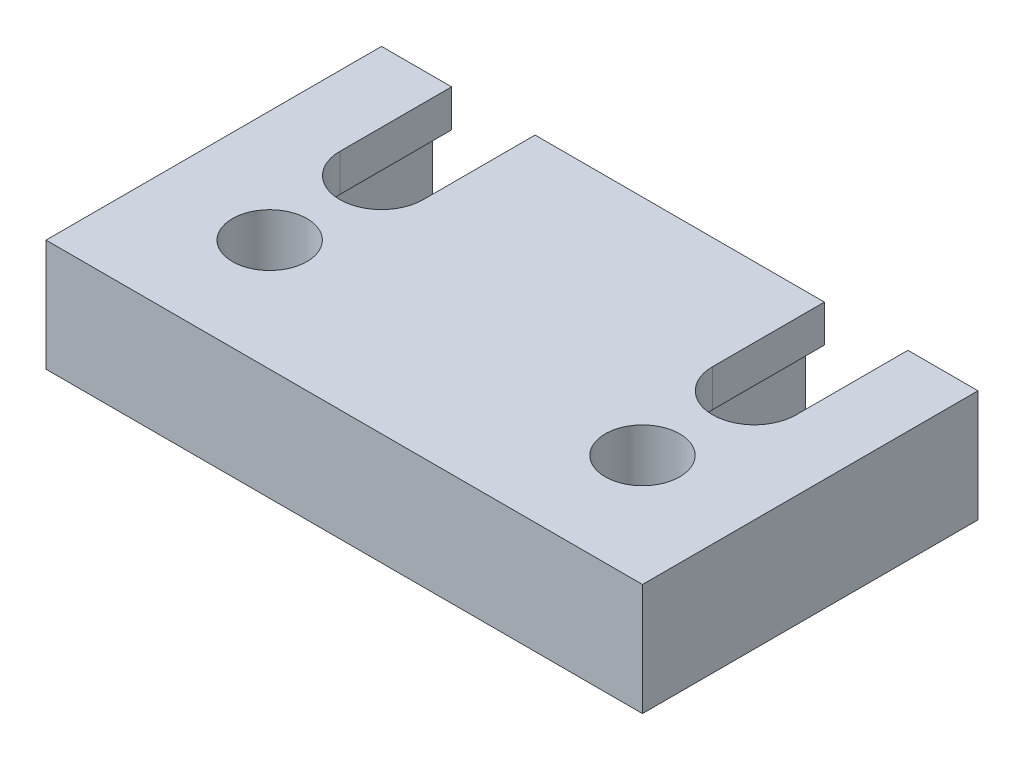
SolidWorks part; units mm, degrees
material "AISI 1018 Steel Cold Rolled"
ref_plane "Plane1" through (0, 0, 0) normal (0, 0, 1) x (1, 0, 0)
ref_plane "Plane2" through (0, 0, 0) normal (0, 1, 0) x (1, 0, 0)
ref_plane "Plane3" through (0, 0, 0) normal (1, 0, 0) x (0, 0, -1)
sketch "Sketch1" plane through (0, 0, 0) normal (0, 1, 0) x (1, 0, 0)
  line L0 (57.15, 76.2) -> (57.15, 0) construction
  line L1 (0, 0) -> (114.3, 0)
  line L2 (0, 0) -> (0, 76.2)
  line L3 (0, 76.2) -> (114.3, 76.2)
  line L4 (114.3, 0) -> (114.3, 76.2)
  line L5 (96.012, 63.5) -> (96.012, 38.1)
  line L6 (18.288, 63.5) -> (18.288, 38.1)
  line L7 (32.512, 63.5) -> (32.512, 38.1)
  line L8 (81.788, 63.5) -> (81.788, 38.1)
  line L9 (18.288, 50.8) -> (32.512, 50.8) construction
  line L10 (96.012, 50.8) -> (81.788, 50.8) construction
  arc A0 (32.512, 63.5) -> (18.288, 63.5) centre (25.4, 63.5) ccw
  arc A1 (18.288, 38.1) -> (32.512, 38.1) centre (25.4, 38.1) ccw
  arc A4 (96.012, 38.1) -> (81.788, 38.1) centre (88.9, 38.1) cw
  arc A5 (81.788, 63.5) -> (96.012, 63.5) centre (88.9, 63.5) cw
  dimension "D3" = 14.224
  dimension "D7" = 63.5
  dimension "D1" = 76.2
  dimension "D2" = 114.3
  dimension "D4" = 25.4
  dimension "D5" = 25.4
  dimension "D8" = 25.4
extrude "Base-Extrude" add sketch "Sketch1" along normal blind 19.05
hole_wizard "1/2-20 Tapped Hole1" positions "Sketch3" profile "Sketch2" tap size "1/2-20" standard "Ansi Inch" end condition through all
sketch "Sketch3" plane through (0, 19.05, 0) normal (0, 1, 0) x (-1, 0, 0)
  line L0 (0, 0) -> (-114.3, 0) construction
  line L2 (-114.3, 0) -> (-114.3, -76.2) construction
  point P0 (-25.4, -19.05)
  point P1 (-88.9, -19.05)
  dimension "D1" = 19.05
  dimension "D2" = 19.05
  dimension "D3" = 88.9
  dimension "D4" = 25.4
sketch "Sketch2" plane through (25.4, 19.05, -19.05) normal (1, 0, 0) x (0, 0, 1)
  line L0 (0, 0) -> (0, 19.05)
  line L1 (0, 19.05) -> (6.35, 19.05)
  line L2 (6.35, 19.05) -> (6.35, 0)
  line L5 (6.35, 0) -> (0, 0)
  line L11 (0, -6.35) -> (0, 107.95) construction
  dimension "Thread Major Dia." = 12.7
  dimension "Thru Tap Drill Depth" = 19.05
ref_plane "Plane4" through (133.35, 0, 0) normal (1, 0, 0) x (0, 0, -1)
sketch "Sketch4" plane through (0, 0, 0) normal (0, -1, 0) x (1, 0, 0)
  line L0 (0, -76.2) -> (0, 0) construction
  line L4 (15.0749, -63.5) -> (15.0749, -38.1)
  line L5 (35.7251, -38.1) -> (35.7251, -63.5)
  arc A4 (35.7251, -38.1) -> (15.0749, -38.1) centre (25.4, -38.1) ccw
  arc A5 (15.0749, -63.5) -> (35.7251, -63.5) centre (25.4, -63.5) ccw
  dimension "D1" = 25.4
extrude "Cut-Extrude1" cut sketch "Sketch4" against normal blind 12.7
sketch "Sketch5" plane through (0, 0, 0) normal (0, -1, 0) x (1, 0, 0)
  line L4 (99.2251, -38.1) -> (99.2251, -63.5)
  line L5 (78.5749, -63.5) -> (78.5749, -38.1)
  arc A4 (78.5749, -63.5) -> (99.2251, -63.5) centre (88.9, -63.5) ccw
  arc A5 (99.2251, -38.1) -> (78.5749, -38.1) centre (88.9, -38.1) ccw
extrude "Cut-Extrude2" cut sketch "Sketch5" against normal blind 12.7
sketch "Sketch7" plane through (0, 0, 0) normal (0, -1, 0) x (1, 0, 0)
  line L2 (107.95, 0) -> (107.95, -76.2)
  line L3 (107.95, 15.9678) -> (107.95, -89.1916)
  dimension "D1" = 6.35
sketch "Sketch8" plane through (0, 0, 0) normal (0, -1, 0) x (1, 0, 0)
  line L2 (6.35, -76.2) -> (6.35, 0)
  line L3 (6.35, -87.7035) -> (6.35, 17.952)
  dimension "D1" = 6.35
extrude "Cut-Extrude3" cut sketch "Sketch7" against normal through all and the other way through all
extrude "Cut-Extrude4" cut sketch "Sketch8" against normal through all and the other way through all
sketch "Sketch9" plane through (0, 0, 0) normal (0, -1, 0) x (1, 0, 0)
  line L2 (107.95, -57.15) -> (6.35, -57.15)
  line L3 (107.95, -57.15) -> (6.35, -57.15)
  dimension "D1" = 19.05
extrude "Cut-Extrude5" cut sketch "Sketch9" against normal through all and the other way through all
